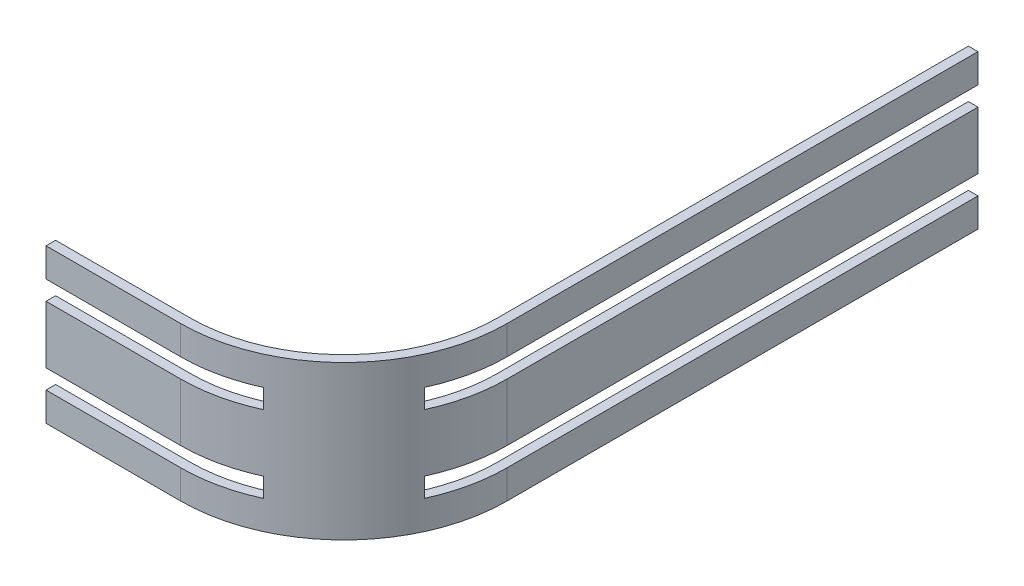
SolidWorks part; units mm, degrees
ref_plane "Front Plane" through (0, 0, 0) normal (0, 0, 1) x (1, 0, 0)
ref_plane "Top Plane" through (0, 0, 0) normal (0, 1, 0) x (1, 0, 0)
ref_plane "Right Plane" through (0, 0, 0) normal (1, 0, 0) x (0, 0, -1)
sketch "Sketch1" plane through (0, 0, 0) normal (0, 1, 0) x (1, 0, 0)
  line L0 (15, 32.5) -> (15, -16.5)
  line L1 (-1, -32.5) -> (-15, -32.5)
  line L2 (-15, -32.5) -> (-15, -33.5)
  line L3 (-15, -33.5) -> (-1, -33.5)
  line L4 (16, -16.5) -> (16, 32.5)
  line L5 (16, 32.5) -> (15, 32.5)
  arc A0 (15, -16.5) -> (-1, -32.5) centre (-1, -16.5) cw
  arc A1 (16, -16.5) -> (-1, -33.5) centre (-1, -16.5) cw
  dimension "D7" = 16
  dimension "D8" = 17
  dimension "D1" = 30
  dimension "D2" = 65
  dimension "D3" = 15
  dimension "D4" = 32.5
  dimension "D5" = 1
  dimension "D6" = 1
extrude "Extrude1" add sketch "Sketch1" along normal mid plane 6
sketch "Sketch2" plane through (0, 3, 0) normal (0, 1, 0) x (1, 0, 0)
  line L0 (6.075, -30.8508) -> (6.075, -31.9578)
  line L1 (13.3508, -23.575) -> (14.4578, -23.575)
  line L2 (15, 32.5) -> (15, -16.5) construction
  line L3 (-1, -32.5) -> (-15, -32.5) construction
  arc A0 (-1, -33.5) -> (16, -16.5) centre (-1, -16.5) ccw construction
  arc A1 (-1, -32.5) -> (15, -16.5) centre (-1, -16.5) ccw construction
  arc A2 (6.075, -31.9578) -> (14.4578, -23.575) centre (-1, -16.5) ccw
  arc A3 (6.075, -30.8508) -> (13.3508, -23.575) centre (-1, -16.5) ccw
  dimension "D1" = 8.925
  dimension "D2" = 8.925
extrude "Extrude2" add sketch "Sketch2" along normal blind 2
sketch "Sketch3" plane through (0, -3, 0) normal (0, -1, 0) x (1, 0, 0)
  line L0 (6.075, 31.9578) -> (6.075, 30.8508)
  line L1 (13.3508, 23.575) -> (14.4578, 23.575)
  line L2 (15, -32.5) -> (15, 16.5) construction
  line L3 (-1, 32.5) -> (-15, 32.5) construction
  arc A0 (16, 16.5) -> (-1, 33.5) centre (-1, 16.5) ccw construction
  arc A1 (15, 16.5) -> (-1, 32.5) centre (-1, 16.5) ccw construction
  arc A2 (14.4578, 23.575) -> (6.075, 31.9578) centre (-1, 16.5) ccw
  arc A3 (13.3508, 23.575) -> (6.075, 30.8508) centre (-1, 16.5) ccw
  dimension "D1" = 8.925
  dimension "D2" = 8.925
extrude "Extrude3" add sketch "Sketch3" along normal blind 2
sketch "Sketch4" plane through (0, -5, 0) normal (0, -1, 0) x (1, 0, 0)
  line L0 (16, -32.5) -> (15, -32.5) construction
  line L1 (16, 16.5) -> (16, -32.5) construction
  line L2 (15, -32.5) -> (15, 16.5) construction
  line L3 (-15, 32.5) -> (-15, 33.5) construction
  line L4 (-1, 32.5) -> (-15, 32.5) construction
  line L5 (-15, 33.5) -> (-1, 33.5) construction
  line L6 (16, -32.5) -> (15, -32.5)
  line L7 (16, 16.5) -> (16, -32.5)
  line L8 (15, -32.5) -> (15, 16.5)
  line L9 (-15, 32.5) -> (-15, 33.5)
  line L10 (-1, 32.5) -> (-15, 32.5)
  line L11 (-15, 33.5) -> (-1, 33.5)
  arc A0 (15, 16.5) -> (13.3508, 23.575) centre (-1, 16.5) ccw construction
  arc A1 (16, 16.5) -> (14.4578, 23.575) centre (-1, 16.5) ccw construction
  arc A2 (13.3508, 23.575) -> (6.075, 30.8508) centre (-1, 16.5) ccw construction
  arc A3 (14.4578, 23.575) -> (6.075, 31.9578) centre (-1, 16.5) ccw construction
  arc A4 (6.075, 31.9578) -> (-1, 33.5) centre (-1, 16.5) ccw construction
  arc A5 (6.075, 30.8508) -> (-1, 32.5) centre (-1, 16.5) ccw construction
  arc A6 (15, 16.5) -> (13.3508, 23.575) centre (-1, 16.5) ccw
  arc A7 (16, 16.5) -> (14.4578, 23.575) centre (-1, 16.5) ccw
  arc A8 (13.3508, 23.575) -> (6.075, 30.8508) centre (-1, 16.5) ccw
  arc A9 (14.4578, 23.575) -> (6.075, 31.9578) centre (-1, 16.5) ccw
  arc A10 (6.075, 31.9578) -> (-1, 33.5) centre (-1, 16.5) ccw
  arc A11 (6.075, 30.8508) -> (-1, 32.5) centre (-1, 16.5) ccw
extrude "Extrude4" add sketch "Sketch4" along normal blind 3
sketch "Sketch5" plane through (0, 5, 0) normal (0, 1, 0) x (1, 0, 0)
  line L0 (16, 32.5) -> (15, 32.5) construction
  line L1 (16, -16.5) -> (16, 32.5) construction
  line L2 (15, 32.5) -> (15, -16.5) construction
  line L3 (-15, -33.5) -> (-1, -33.5) construction
  line L4 (-1, -32.5) -> (-15, -32.5) construction
  line L5 (-15, -32.5) -> (-15, -33.5) construction
  line L6 (16, 32.5) -> (15, 32.5)
  line L7 (16, -16.5) -> (16, 32.5)
  line L8 (15, 32.5) -> (15, -16.5)
  line L9 (-15, -33.5) -> (-1, -33.5)
  line L10 (-1, -32.5) -> (-15, -32.5)
  line L11 (-15, -32.5) -> (-15, -33.5)
  arc A0 (13.3508, -23.575) -> (15, -16.5) centre (-1, -16.5) ccw construction
  arc A1 (14.4578, -23.575) -> (16, -16.5) centre (-1, -16.5) ccw construction
  arc A2 (6.075, -31.9578) -> (14.4578, -23.575) centre (-1, -16.5) ccw construction
  arc A3 (6.075, -30.8508) -> (13.3508, -23.575) centre (-1, -16.5) ccw construction
  arc A4 (-1, -32.5) -> (6.075, -30.8508) centre (-1, -16.5) ccw construction
  arc A5 (-1, -33.5) -> (6.075, -31.9578) centre (-1, -16.5) ccw construction
  arc A6 (13.3508, -23.575) -> (15, -16.5) centre (-1, -16.5) ccw
  arc A7 (14.4578, -23.575) -> (16, -16.5) centre (-1, -16.5) ccw
  arc A8 (6.075, -31.9578) -> (14.4578, -23.575) centre (-1, -16.5) ccw
  arc A9 (6.075, -30.8508) -> (13.3508, -23.575) centre (-1, -16.5) ccw
  arc A10 (-1, -32.5) -> (6.075, -30.8508) centre (-1, -16.5) ccw
  arc A11 (-1, -33.5) -> (6.075, -31.9578) centre (-1, -16.5) ccw
extrude "Extrude5" add sketch "Sketch5" along normal blind 3
